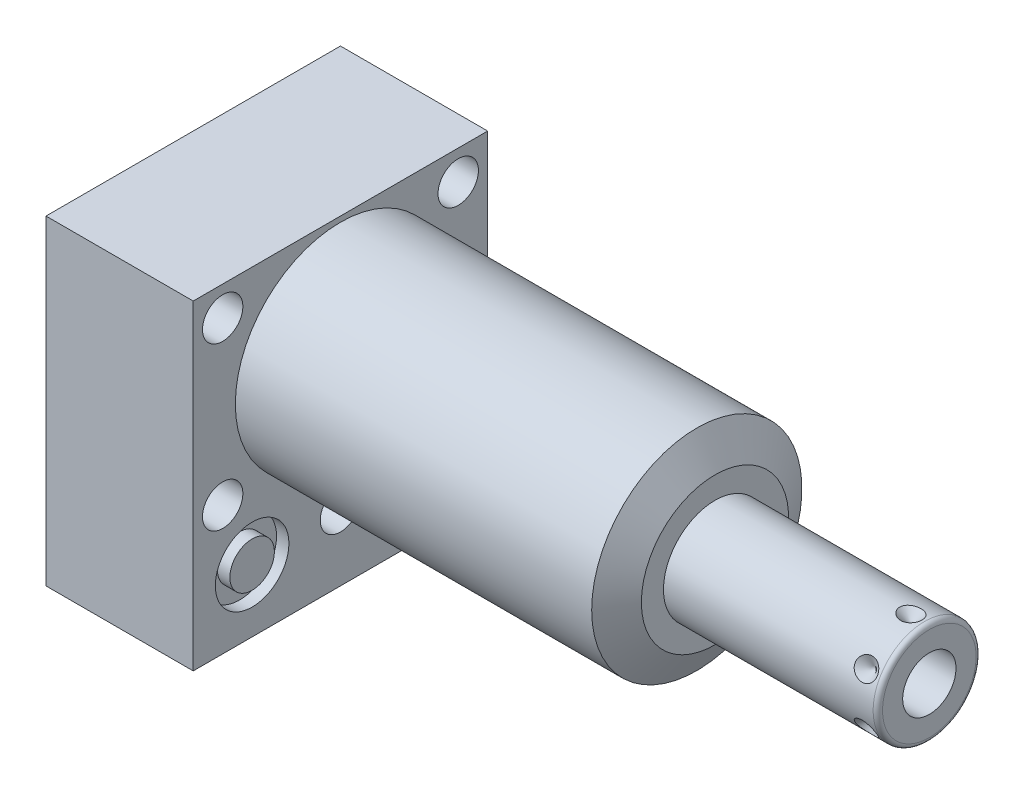
SolidWorks part; units mm, degrees
material "Alloy Steel"
ref_plane "Front Plane" through (0, 0, 0) normal (0, 0, 1) x (1, 0, 0)
ref_plane "Top Plane" through (0, 0, 0) normal (0, 1, 0) x (1, 0, 0)
ref_plane "Right Plane" through (0, 0, 0) normal (1, 0, 0) x (0, 0, -1)
ref_plane "Plane1" through (0, 0, 0) normal (1, 0, 0) x (0, 0, -1)
sketch "Sketch1" plane through (0, 0, 0) normal (1, 0, 0) x (0, 0, -1)
  line L0 (-31.75, 23.8252) -> (-31.75, -45.2628)
  line L1 (-31.75, -45.2628) -> (31.75, -45.2628)
  line L2 (31.75, -45.2628) -> (31.75, 23.8252)
  line L3 (31.75, 23.8252) -> (-31.75, 23.8252)
  line L4 (0, -55.6514) -> (0, 27.6098) construction
  dimension "D1" = 63.5
  dimension "D2" = 69.088
  dimension "D3" = 23.8252
extrude "Extrude1" add sketch "Sketch1" along normal blind 80.772 and the other way blind 31.75
ref_plane "Plane2" through (0, 0, 0) normal (1, 0, 0) x (0, 0, -1)
sketch "Sketch2" plane through (0, 0, 0) normal (1, 0, 0) x (0, 0, -1)
  line L0 (-26.0541, 0) -> (26.0541, 0) construction
  line L5 (31.75, 23.8252) -> (-31.75, 23.8252)
  line L6 (-31.75, 23.8252) -> (-31.75, -45.2628)
  line L7 (-31.75, -45.2628) -> (31.75, -45.2628)
  line L8 (31.75, -45.2628) -> (31.75, 23.8252)
  line L9 (31.75, 23.8252) -> (-31.75, 23.8252)
  line L10 (-31.75, 23.8252) -> (-31.75, -45.2628)
  line L11 (-31.75, -45.2628) -> (31.75, -45.2628)
  line L12 (31.75, -45.2628) -> (31.75, 23.8252)
  circle A0 centre (0, 0) radius 22.6695
  dimension "D1" = 45.339
  dimension "D2" = 0
extrude "Cut-Extrude1" cut sketch "Sketch2" along normal up to next
ref_plane "Plane3" through (0, 0, 0) normal (0, 0, 1) x (1, 0, 0)
sketch "Sketch3" plane through (0, 0, 0) normal (0, 0, 1) x (1, 0, 0)
  line L0 (76.8492, 22.6695) -> (80.772, 15.875)
  line L1 (76.0371, 0) -> (80.9975, 0) construction
  line L2 (80.772, 22.6695) -> (80.772, 15.875)
  line L3 (80.772, 22.6695) -> (76.8492, 22.6695)
  line L4 (80.772, 22.6695) -> (0, 22.6695) construction
  line L5 (80.772, -22.6695) -> (80.772, 22.6695) construction
  dimension "D1" = 31.75
  dimension "D2" = 30
revolve "Cut-Revolve1" cut sketch "Sketch3" angle 360 about L1
ref_plane "Plane4" through (-29.083, -31.75, 19.05) normal (0, 0, 1) x (0, 1, 0)
sketch "S2D0002" plane through (-29.083, -31.75, 19.05) normal (0, 0, 1) x (0, 1, 0)
  line L0 (0, 0) -> (4.5466, 0)
  line L1 (4.5466, 0) -> (4.1066, -2.0701)
  line L2 (4.1066, -2.0701) -> (3.4544, -2.7223)
  line L3 (3.4544, -2.7223) -> (3.4544, -13.97)
  line L4 (3.4544, -13.97) -> (0, -13.97)
  line L5 (0, -13.97) -> (0, 0)
  line L6 (0, -14.6685) -> (0, 0.6985) construction
  dimension "D1" = 13.97
revolve "Cut-Revolve2" cut sketch "S2D0002" angle 360 about L6
ref_plane "Plane5" through (-29.083, -31.75, -19.05) normal (0, 0, 1) x (0, 1, 0)
sketch "Sketch5" plane through (-29.083, -31.75, -19.05) normal (0, 0, 1) x (0, 1, 0)
  line L0 (0, 0) -> (4.5466, 0)
  line L1 (4.5466, 0) -> (4.1066, -2.0701)
  line L2 (4.1066, -2.0701) -> (3.4544, -2.7223)
  line L3 (3.4544, -2.7223) -> (3.4544, -13.97)
  line L4 (3.4544, -13.97) -> (0, -13.97)
  line L5 (0, -13.97) -> (0, 0)
  line L6 (0, -14.6685) -> (0, 0.6985) construction
  dimension "D1" = 13.97
revolve "Cut-Revolve3" cut sketch "Sketch5" angle 360 about L6
ref_plane "Plane6" through (-2.667, -31.75, 19.05) normal (0, 0, 1) x (0, -1, 0)
sketch "Sketch6" plane through (-2.667, -31.75, 19.05) normal (0, 0, 1) x (0, -1, 0)
  line L0 (0, 0) -> (4.5466, 0)
  line L1 (4.5466, 0) -> (4.1066, -2.0701)
  line L2 (4.1066, -2.0701) -> (3.4544, -2.7223)
  line L3 (3.4544, -2.7223) -> (3.4544, -12.192)
  line L4 (3.4544, -12.192) -> (0, -12.192)
  line L5 (0, -12.192) -> (0, 0)
  line L6 (0, -12.8016) -> (0, 0.6096) construction
  dimension "D1" = 12.192
revolve "Cut-Revolve4" cut sketch "Sketch6" angle 360 about L6
ref_plane "Plane7" through (-2.667, -31.75, -19.05) normal (0, 0, 1) x (0, -1, 0)
sketch "Sketch7" plane through (-2.667, -31.75, -19.05) normal (0, 0, 1) x (0, -1, 0)
  line L0 (0, 0) -> (4.5466, 0)
  line L1 (4.5466, 0) -> (4.1066, -2.0701)
  line L2 (4.1066, -2.0701) -> (3.4544, -2.7223)
  line L3 (3.4544, -2.7223) -> (3.4544, -12.192)
  line L4 (3.4544, -12.192) -> (0, -12.192)
  line L5 (0, -12.192) -> (0, 0)
  line L6 (0, -12.8016) -> (0, 0.6096) construction
  dimension "D1" = 12.192
revolve "Cut-Revolve5" cut sketch "Sketch7" angle 360 about L6
ref_plane "Plane8" through (-15.875, -51.6128, 19.05) normal (0, 0, 1) x (-1, 0, 0)
sketch "Sketch8" plane through (-15.875, -51.6128, 19.05) normal (0, 0, 1) x (-1, 0, 0)
  line L0 (0, -6.604) -> (6.1849, -6.604)
  line L1 (6.1849, -6.604) -> (5.6423, -9.1567)
  line L2 (5.6423, -9.1567) -> (4.9784, -9.8206)
  line L3 (4.9784, -9.8206) -> (4.9784, -25.654)
  line L4 (4.9784, -25.654) -> (0, -25.654)
  line L5 (0, -25.654) -> (0, -6.604)
  line L6 (0, -26.67) -> (0, 1.27) construction
  line L7 (15.875, -6.35) -> (-15.875, -6.35) construction
  dimension "D1" = 19.05
  dimension "D2" = 0.254
revolve "Cut-Revolve6" cut sketch "Sketch8" angle 360 about L6
ref_plane "Plane9" through (-15.875, -51.6128, -19.05) normal (0, 0, 1) x (-1, 0, 0)
sketch "Sketch9" plane through (-15.875, -51.6128, -19.05) normal (0, 0, 1) x (-1, 0, 0)
  line L0 (0, -6.604) -> (6.1849, -6.604)
  line L1 (6.1849, -6.604) -> (5.6423, -9.1567)
  line L2 (5.6423, -9.1567) -> (4.9784, -9.8206)
  line L3 (4.9784, -9.8206) -> (4.9784, -25.654)
  line L4 (4.9784, -25.654) -> (0, -25.654)
  line L5 (0, -25.654) -> (0, -6.604)
  line L6 (0, -26.67) -> (0, 1.27) construction
  line L7 (15.875, -6.35) -> (-15.875, -6.35) construction
  dimension "D1" = 19.05
  dimension "D2" = 0.254
revolve "Cut-Revolve7" cut sketch "Sketch9" angle 360 about L6
ref_plane "Plane10" through (0, 0, 0) normal (0, 0, 1) x (1, 0, 0)
sketch "Sketch18" plane through (0, 0, 0) normal (1, 0, 0) x (0, 0, -1)
  circle A0 centre (-19.05, -31.75) radius 7.9375
  circle A1 centre (19.05, -31.75) radius 7.9375
  dimension "D1" = 15.875
extrude "Cut-Extrude2" cut sketch "Sketch18" against normal blind 2.667
sketch "Sketch19" plane through (-31.75, 0, 0) normal (-1, 0, 0) x (0, 0, 1)
  circle A0 centre (-19.05, -31.75) radius 7.9375
  circle A1 centre (19.05, -31.75) radius 7.9375
  dimension "D1" = 15.875
extrude "Cut-Extrude3" cut sketch "Sketch19" against normal blind 2.667
sketch "Sketch20" plane through (0, -45.2628, 0) normal (0, -1, 0) x (1, 0, 0)
  circle A0 centre (-15.875, -19.05) radius 9.525
  circle A1 centre (-15.875, 19.05) radius 9.525
  circle A2 centre (-15.875, 19.05) radius 6.1849 construction
  dimension "D1" = 19.05
extrude "Cut-Extrude4" cut sketch "Sketch20" against normal blind 0.254
sketch "Sketch10" plane through (0, 0, 0) normal (0, 0, 1) x (1, 0, 0)
  line L0 (80.772, 0) -> (80.772, 11.1125)
  line L1 (80.772, 11.1125) -> (125.984, 11.1125)
  line L2 (127, 10.0965) -> (127, 0)
  line L3 (127, 0) -> (80.772, 0)
  line L4 (58.2708, 0) -> (120.537, 0) construction
  line L5 (80.772, -15.875) -> (80.772, 15.875) construction
  line L6 (-31.75, 23.8252) -> (-31.75, -45.2628) construction
  arc A0 (127, 10.0965) -> (125.984, 11.1125) centre (125.984, 10.0965) ccw
  point P0 (80.772, 0)
  dimension "D2" = 1.016
  dimension "D1" = 22.225
  dimension "D3" = 158.75
revolve "Revolve1" add sketch "Sketch10" angle 360 about L4
ref_plane "Plane11" through (118.6434, -5.7531, 0) normal (0, 0, 1) x (0, -1, 0)
sketch "S2D0001" plane through (118.6434, -5.7531, 0) normal (0, 0, 1) x (0, -1, 0)
  line L0 (0, 8.3566) -> (0, -8.6614)
  line L1 (0, -8.6614) -> (-5.7531, -12.1182)
  line L2 (0, 8.3566) -> (-5.7531, 8.3566)
  line L3 (-5.7531, 8.3566) -> (-5.7531, -12.1182)
  line L4 (-5.7531, -34.3471) -> (-5.7531, 1.0237) construction
  line L5 (4.3434, 8.3566) -> (-15.8496, 8.3566) construction
  dimension "D1" = 11.5062
  dimension "D2" = 17.018
  dimension "D3" = 59
revolve "Cut-Revolve8" cut sketch "S2D0001" angle 360 about L4
ref_plane "Plane12" through (-31.75, -51.6128, 0) normal (0, -1, 0) x (0, 0, -1)
sketch "Sketch12" plane through (-31.75, -45.0088, 0) normal (0, -1, 0) x (0, 0, -1)
  circle A0 centre (-19.05, 15.875) radius 6.4389
  circle A1 centre (-19.05, 15.875) radius 9.525 construction
  dimension "D1" = 12.8778
extrude "Extrude2" add sketch "Sketch12" along normal blind 1.651
sketch "Sketch13" plane through (0, 0, 0) normal (1, 0, 0) x (0, 0, -1)
  circle A0 centre (-19.05, -31.75) radius 4.8006
  circle A1 centre (-19.05, -31.75) radius 7.9375 construction
  dimension "D1" = 9.6012
ref_plane "Plane13" through (-31.75, 0, 0) normal (1, 0, 0) x (0, 0, -1)
extrude "Extrude3" add sketch "Sketch13" along normal up to surface
ref_plane "Plane14" through (0, -31.75, -19.05) normal (0, -1, 0) x (0, 0, -1)
sketch "Sketch14" plane through (0, -31.75, -19.05) normal (0, -1, 0) x (0, 0, -1)
  line L0 (0, -2.8435) -> (0, 1.0401) construction
  line L1 (0, -5.3893) -> (0, -12.2901) construction
  line L2 (7.9375, -2.667) -> (-7.9375, -2.667) construction
  circle A0 centre (6.1722, -0.9017) radius 1.7653
  dimension "D1" = 3.5306
  dimension "D2" = 12.3444
revolve "Revolve2" add sketch "Sketch14" angle 360 about L0
ref_plane "Plane15" through (0, -31.75, -19.05) normal (0, -1, 0) x (0, 0, -1)
sketch "Sketch15" plane through (0, -31.75, -19.05) normal (0, -1, 0) x (0, 0, -1)
  line L0 (0, -32.7901) -> (0, -28.9065) construction
  line L1 (0, -29.083) -> (0, -27.0129) construction
  line L2 (-7.9375, -29.083) -> (7.9375, -29.083) construction
  circle A0 centre (6.1722, -30.8483) radius 1.7653
  dimension "D1" = 3.5306
  dimension "D2" = 12.3444
revolve "Revolve3" add sketch "Sketch15" angle 360 about L0
ref_plane "Plane16" through (114.681, -11.1125, 0) normal (0, 0, 1) x (-1, 0, 0)
sketch "Sketch16" plane through (114.681, -11.1125, 0) normal (0, 0, 1) x (-1, 0, 0)
  line L0 (-8.3566, 0) -> (-5.9436, 0)
  line L1 (-5.9436, 0) -> (-8.3566, -2.413)
  line L2 (-8.3566, 0) -> (-8.3566, -2.413)
  line L3 (-8.3566, -5.0193) -> (-8.3566, 0.1207) construction
  line L4 (33.909, 0) -> (-11.303, 0) construction
  line L5 (-12.319, -1.016) -> (-12.319, -21.209) construction
  dimension "D1" = 3.9624
  dimension "D2" = 4.826
  dimension "D3" = 45
ref_plane "Plane17" through (114.681, 11.1125, 0) normal (0, 0, 1) x (1, 0, 0)
revolve "Cut-Revolve9" cut sketch "Sketch16" angle 360 about L3
pattern_circular "CirPattern1" count 6 over 360 of "Cut-Revolve9"
hole_wizard "Hole1" positions "Sketch22" profile "Sketch21" legacy end condition up to next
sketch "Sketch22" plane through (0, 0, 0) normal (1, 0, 0) x (0, 0, -1)
  line L0 (0, 0) -> (-38.8053, 0) construction
  line L1 (0, 0) -> (0, 31.2017) construction
  point P0 (-25.4, 17.4752)
  point P1 (0, -30.8356)
  point P12 (-25.4, -17.4752)
  point P14 (25.4, 17.4752)
  point P15 (25.4, -17.4752)
  dimension "D1" = 25.4
  dimension "D2" = 17.4752
  dimension "D3" = 30.8356
sketch "Sketch21" plane through (0, 17.4752, 25.4) normal (0, 1, 0) x (0, 0, -1)
  line L0 (0, 0) -> (0, 31.75)
  line L1 (0, 31.75) -> (4.3561, 31.75)
  line L2 (4.3561, 31.75) -> (4.3561, 0)
  line L3 (4.3561, 0) -> (0, 0)
  line L4 (0, 110) -> (0, -10) construction
  dimension "Diameter" = 8.7122
  dimension "Depth" = 31.75
